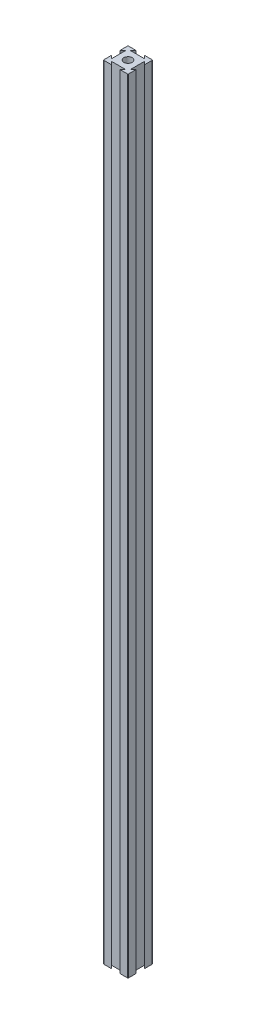
SolidWorks part; units mm, degrees
material "Alumina"
ref_plane "Front Plane" through (0, 0, 0) normal (0, 0, 1) x (1, 0, 0)
ref_plane "Top Plane" through (0, 0, 0) normal (0, 1, 0) x (1, 0, 0)
ref_plane "Right Plane" through (0, 0, 0) normal (1, 0, 0) x (0, 0, -1)
sketch "Sketch1" plane through (0, 0, 0) normal (0, 1, 0) x (1, 0, 0)
  line L0 (6.6667, 20) -> (4.285, 17.6183)
  line L1 (0, 0) -> (20, 0)
  line L2 (0, 0) -> (0, 20)
  line L3 (0, 20) -> (20, 20)
  line L4 (20, 0) -> (20, 20)
  line L5 (4.285, 17.6183) -> (15.715, 17.6183)
  line L6 (15.715, 17.6183) -> (13.3333, 20)
  line L7 (13.3333, 20) -> (6.6667, 20)
  line L8 (0, 10) -> (20, 10) construction
  line L9 (10, 20) -> (10, 0) construction
  line L10 (15.715, 2.3817) -> (13.3333, 0)
  line L11 (4.285, 2.3817) -> (15.715, 2.3817)
  line L12 (6.6667, 0) -> (4.285, 2.3817)
  line L13 (13.3333, 0) -> (6.6667, 0)
  line L14 (0, 13.3333) -> (2.3817, 15.715)
  line L15 (2.3817, 15.715) -> (2.3817, 4.285)
  line L16 (2.3817, 4.285) -> (0, 6.6667)
  line L17 (0, 6.6667) -> (0, 13.3333)
  line L18 (17.6183, 4.285) -> (20, 6.6667)
  line L19 (17.6183, 15.715) -> (17.6183, 4.285)
  line L20 (20, 13.3333) -> (17.6183, 15.715)
  line L21 (20, 6.6667) -> (20, 13.3333)
  circle A0 centre (10, 10) radius 3.3333
  dimension "D1" = 20
  dimension "D2" = 20
  dimension "D3" = 6.6667
  dimension "D4" = 6.6667
  dimension "D5" = 45
  dimension "D6" = 45
  dimension "D7" = 11.43
  dimension "D8" = 6.6667
  dimension "D9" = 6.6667
  dimension "D10" = 11.43
  dimension "D11" = 45
  dimension "D12" = 45
extrude "Boss-Extrude1" add sketch "Sketch1" along normal blind 635 contours L20 L4 L3 L6 L5 L0 L2 L14 L15 L16 L1 L12 L11 L10 L18 L19 A0
fillet "Fillet4" radius 0.508 4 edges at (0, 317.5, -20) (20, 317.5, -20) (0, 317.5, 0) (20, 317.5, 0)
